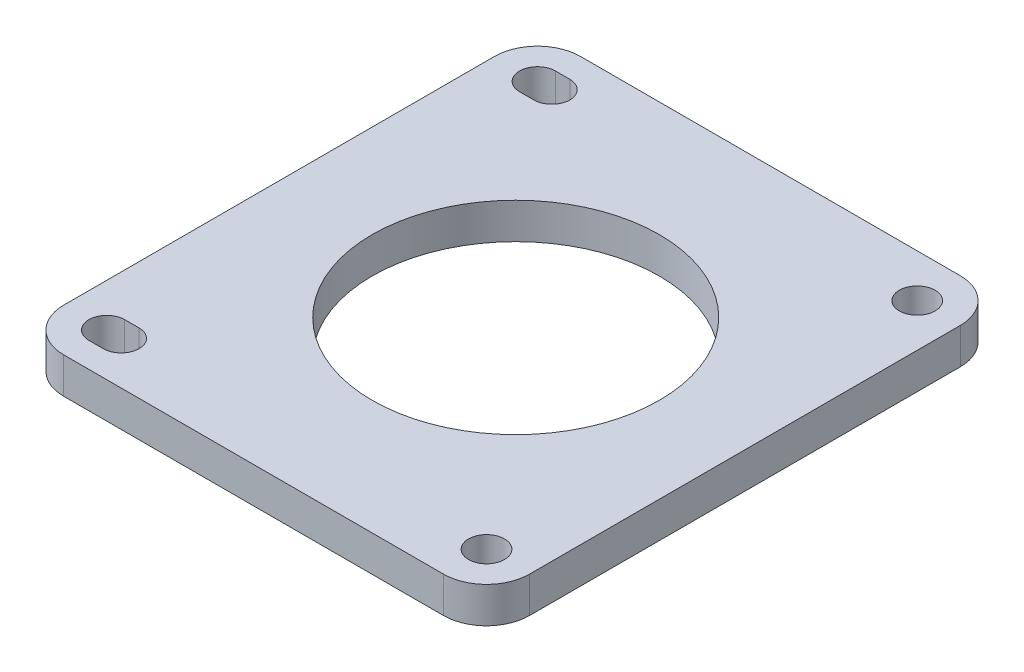
SolidWorks part; units mm, degrees
ref_plane "Front Plane" through (0, 0, 0) normal (0, 0, 1) x (1, 0, 0)
ref_plane "Top Plane" through (0, 0, 0) normal (0, 1, 0) x (1, 0, 0)
ref_plane "Right Plane" through (0, 0, 0) normal (1, 0, 0) x (0, 0, -1)
sketch "Sketch1" plane through (0, 0, 0) normal (0, 1, 0) x (1, 0, 0)
  line L0 (6, 3.5) -> (8, 3.5)
  line L1 (6, 0) -> (58.9, 0)
  line L2 (0, 6) -> (0, 66)
  line L3 (6, 72) -> (58.9, 72)
  line L4 (64.9, 6) -> (64.9, 66)
  line L5 (6, 8.5) -> (8, 8.5)
  line L6 (6, 63.5) -> (8, 63.5)
  line L7 (6, 68.5) -> (8, 68.5)
  arc A0 (6, 68.5) -> (6, 63.5) centre (6, 66) ccw
  circle A1 centre (58.9, 66) radius 2.5
  circle A2 centre (58.9, 6) radius 2.5
  arc A3 (6, 8.5) -> (6, 3.5) centre (6, 6) ccw
  arc A4 (8, 3.5) -> (8, 8.5) centre (8, 6) ccw
  arc A5 (8, 63.5) -> (8, 68.5) centre (8, 66) ccw
  circle A6 centre (32.97, 36) radius 20
  arc A7 (6, 0) -> (0, 6) centre (6, 6) cw
  arc A8 (58.9, 0) -> (64.9, 6) centre (58.9, 6) ccw
  arc A9 (58.9, 72) -> (64.9, 66) centre (58.9, 66) cw
  arc A10 (0, 66) -> (6, 72) centre (6, 66) cw
  point P25 (0, 0)
  point P30 (64.9, 72)
  point P33 (0, 72)
  dimension "D3" = 5
  dimension "D4" = 6
  dimension "D5" = 6
  dimension "D6" = 5
  dimension "D7" = 6
  dimension "D8" = 6
  dimension "D9" = 5
  dimension "D10" = 5
  dimension "D11" = 6
  dimension "D12" = 6
  dimension "D13" = 2
  dimension "D14" = 2
  dimension "D17" = 40
  dimension "D18" = 32.97
  dimension "D19" = 36
  dimension "D20" = 6
  dimension "D1" = 64.9
  dimension "D2" = 72
  dimension "D15" = 3.5
  dimension "D16" = 3.5
extrude "Boss-Extrude1" add sketch "Sketch1" along normal blind 5
